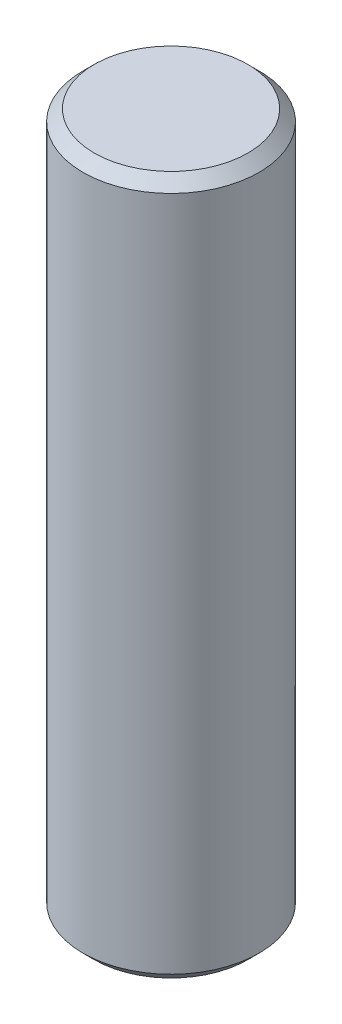
SolidWorks part; units mm, degrees
ref_plane "Front Plane" through (0, 0, 0) normal (0, 0, 1) x (1, 0, 0)
ref_plane "Top Plane" through (0, 0, 0) normal (0, 1, 0) x (1, 0, 0)
ref_plane "Right Plane" through (0, 0, 0) normal (1, 0, 0) x (0, 0, -1)
sketch "Sketch1" plane through (0, 0, 0) normal (0, 1, 0) x (1, 0, 0)
  circle A0 centre (0, 0) radius 4
  dimension "D1" = 8
extrude "Boss-Extrude1" add sketch "Sketch1" along normal blind 31.75
chamfer "Chamfer1" distance 0.508 angle 45 2 edges at (0, 0, 4) (0, 31.75, 4)
